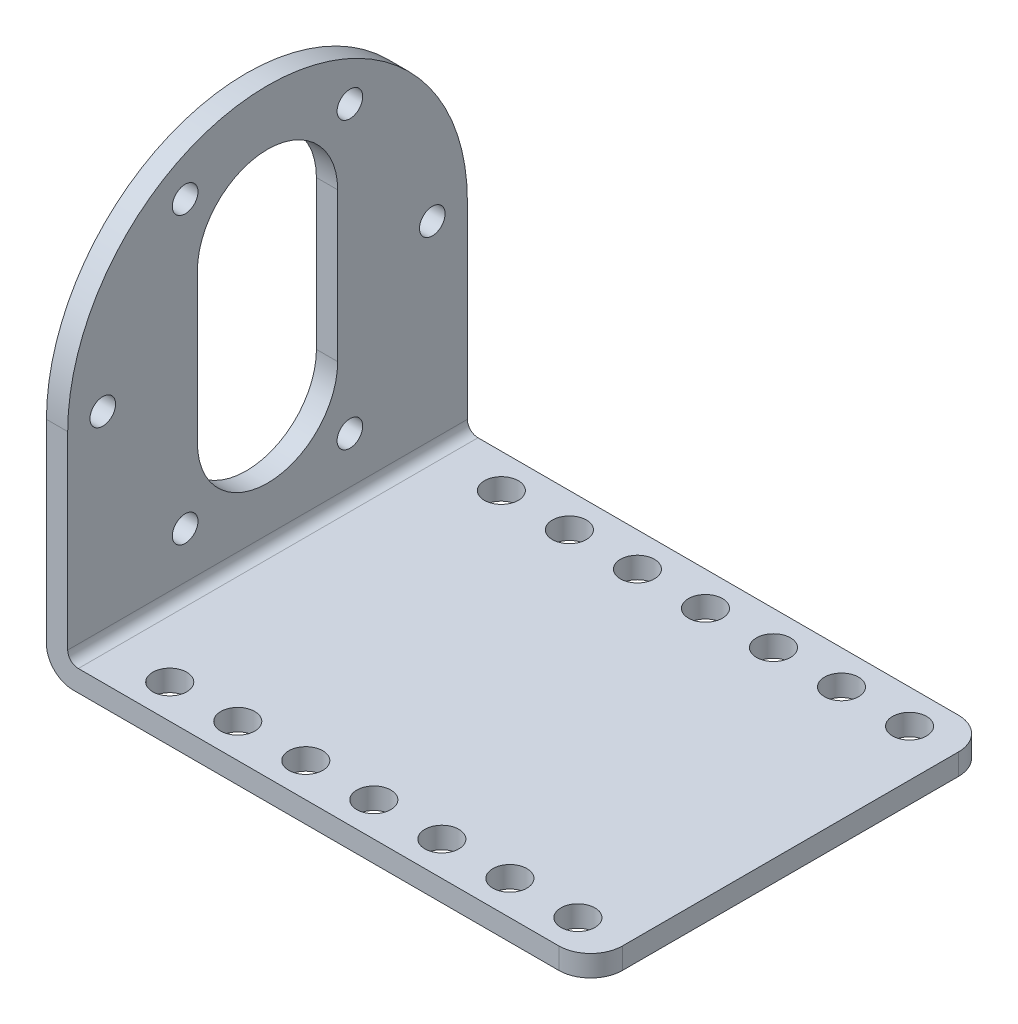
SolidWorks part; units mm, degrees
ref_plane "Front Plane" through (0, 0, 0) normal (0, 0, 1) x (1, 0, 0)
ref_plane "Top Plane" through (0, 0, 0) normal (0, 1, 0) x (1, 0, 0)
ref_plane "Right Plane" through (0, 0, 0) normal (1, 0, 0) x (0, 0, -1)
sketch "Sketch1" plane through (0, 0, 0) normal (0, 0, 1) x (1, 0, 0)
  line L1 (2.5, 0) -> (51.2, 0)
  line L2 (0, 2.5) -> (0, 39.6)
  line L3 (0, 39.6) -> (2, 39.6)
  line L4 (51.2, 0) -> (51.2, 2)
  line L5 (3, 2) -> (51.2, 2)
  line L6 (2, 3) -> (2, 39.6)
  arc A0 (2.5, 0) -> (0, 2.5) centre (2.5, 2.5) cw
  arc A1 (3, 2) -> (2, 3) centre (3, 3) cw
  point P9 (0, 0)
  dimension "D4" = 2.5
  dimension "D5" = 1
  dimension "D1" = 2
  dimension "D2" = 49.2
  dimension "D3" = 37.6
extrude "Boss-Extrude1" add sketch "Sketch1" along normal mid plane 37.6
sketch "Sketch2" plane through (0, 0, 0) normal (-1, 0, 0) x (0, 0, 1)
  line L0 (0, 27.8) -> (0, 13.8) construction
  line L1 (6.6, 27.8) -> (6.6, 13.8)
  line L2 (-6.6, 27.8) -> (-6.6, 13.8)
  line L3 (18.8, 39.6) -> (-18.8, 39.6) construction
  line L4 (-18.8, 39.6) -> (-18.8, 2.5)
  line L5 (-18.8, 2.5) -> (18.8, 2.5)
  line L6 (18.8, 2.5) -> (18.8, 39.6)
  line L7 (18.8, 39.6) -> (-18.8, 39.6)
  line L8 (-18.8, 40.1) -> (-18.8, 20.8)
  line L10 (18.8, 20.8) -> (18.8, 40.1)
  line L12 (-18.8, 40.1) -> (18.8, 40.1)
  arc A0 (18.8, 20.8) -> (-18.8, 20.8) centre (0, 20.8) ccw
  arc A1 (6.6, 27.8) -> (-6.6, 27.8) centre (0, 27.8) ccw
  arc A2 (-6.6, 13.8) -> (6.6, 13.8) centre (0, 13.8) ccw
  circle A3 centre (0, 20.8) radius 15.5 construction
  circle A4 centre (15.5, 20.8) radius 1.2044
  circle A5 centre (7.75, 7.3766) radius 1.2044
  circle A6 centre (-7.75, 7.3766) radius 1.2044
  circle A7 centre (-15.5, 20.8) radius 1.2044
  circle A8 centre (-7.75, 34.2234) radius 1.2044
  circle A9 centre (7.75, 34.2234) radius 1.2044
  point P10 (0, 20.8)
  point P35 (0, 20.8)
  dimension "D2" = 14
  dimension "D4" = 31
  dimension "D5" = 2.4087
  dimension "D3" = 13.2
  dimension "D6" = 0.5
  dimension "D1" = 0
  dimension "D7" = 6
extrude "Cut-Extrude1" cut sketch "Sketch2" against normal up to next
fillet "Fillet1" radius 3 2 edges at (51.2, 1, -18.8) (51.2, 1, 18.8)
hole_wizard "Ø3.2 (3.2) Diameter Hole1" positions "Sketch3" profile "Sketch4" hole size "Ø3.2" standard "ANSI Metric" end condition up to next
sketch "Sketch3" plane through (0, 2, 0) normal (0, 1, 0) x (1, 0, 0)
  line L0 (0, 0) -> (51.2, 0) construction
  line L1 (51.2, -15.8) -> (51.2, 15.8) construction
  line L4 (0, 18.8) -> (0, -18.8) construction
  line L5 (8.4, 15.6) -> (14.8, 15.6) construction
  point P0 (8.4, 15.6)
  point P2 (8.4, -15.6)
  point P22 (14.8, 15.6)
  point P23 (14.8, -15.6)
  point P24 (21.2, 15.6)
  point P25 (21.2, -15.6)
  point P26 (27.6, 15.6)
  point P27 (27.6, -15.6)
  point P28 (34, 15.6)
  point P29 (34, -15.6)
  point P30 (40.4, 15.6)
  point P31 (40.4, -15.6)
  point P32 (46.8, 15.6)
  point P33 (46.8, -15.6)
  dimension "D1" = 8.4
  dimension "D2" = 31.2
  dimension "D4" = 6.4
  dimension "D3" = 7
sketch "Sketch4" plane through (8.4, 2, -15.6) normal (1, 0, 0) x (0, 0, 1)
  line L0 (0, 0) -> (0, 2)
  line L1 (0, 2) -> (1.6, 2)
  line L2 (1.6, 2) -> (1.6, 0)
  line L5 (1.6, 0) -> (0, 0)
  line L11 (0, -6.35) -> (0, 107.95) construction
  dimension "Thru Hole Dia." = 3.2
  dimension "Thru Hole Depth" = 2
